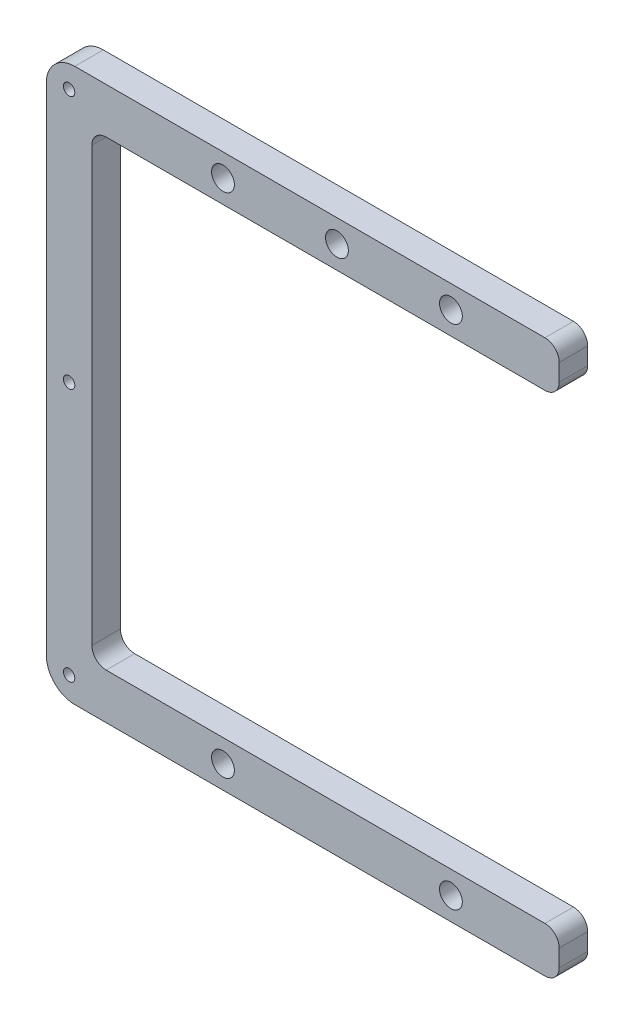
SolidWorks part; units mm, degrees
ref_plane "Front Plane" through (0, 0, 0) normal (0, 0, 1) x (1, 0, 0)
ref_plane "Top Plane" through (0, 0, 0) normal (0, 1, 0) x (1, 0, 0)
ref_plane "Right Plane" through (0, 0, 0) normal (1, 0, 0) x (0, 0, -1)
sketch "Sketch1" plane through (0, 0, 0) normal (0, 0, 1) x (1, 0, 0)
  line L0 (0, -43.5) -> (0, 43.5)
  line L1 (5, 48.5) -> (87.5, 48.5)
  line L2 (90, 46) -> (90, 43)
  line L3 (87.5, 40.5) -> (10.5, 40.5)
  line L4 (8, 38) -> (8, -38)
  line L5 (10.5, -40.5) -> (87.5, -40.5)
  line L7 (87.5, -48.5) -> (5, -48.5)
  line L8 (90, -43) -> (90, -46)
  arc A0 (0, -43.5) -> (5, -48.5) centre (5, -43.5) ccw
  arc A1 (0, 43.5) -> (5, 48.5) centre (5, 43.5) cw
  arc A2 (90, 43) -> (87.5, 40.5) centre (87.5, 43) cw
  arc A3 (87.5, 48.5) -> (90, 46) centre (87.5, 46) cw
  arc A6 (8, -38) -> (10.5, -40.5) centre (10.5, -38) ccw
  arc A7 (10.5, 40.5) -> (8, 38) centre (10.5, 38) ccw
  arc A8 (90, -46) -> (87.5, -48.5) centre (87.5, -46) cw
  arc A9 (90, -43) -> (87.5, -40.5) centre (87.5, -43) ccw
  point P4 (0, 0)
  dimension "D6" = 5
  dimension "D7" = 2.5
  dimension "D9" = 2.5
  dimension "D1" = 89
  dimension "D2" = 8
  dimension "D3" = 8
  dimension "D4" = 8
  dimension "D5" = 90
  dimension "D8" = 0
extrude "Boss-Extrude1" add sketch "Sketch1" along normal blind 5
sketch "Sketch4" plane through (0, 0, 5) normal (0, 0, 1) x (1, 0, 0)
  line L0 (51, 52.0993) -> (51, -52.0993) construction
  line L2 (90, 43) -> (90, 46) construction
  line L3 (90, 44.5) -> (10.5, 44.5) construction
  line L4 (0, 0) -> (111.1347, 0) construction
  line L6 (0, 43.5) -> (0, -43.5) construction
  circle A0 centre (71, 44.5) radius 2
  circle A1 centre (31, 44.5) radius 2
  circle A2 centre (71, -44.5) radius 2
  circle A3 centre (31, -44.5) radius 2
  circle A4 centre (51, 44.5) radius 2
  dimension "D2" = 4
  dimension "D3" = 4
  dimension "D6" = 4
  dimension "D1" = 51
  dimension "D4" = 40
  dimension "D5" = 31
extrude "Cut-Extrude1" cut sketch "Sketch4" against normal through all
sketch "Sketch5" plane through (0, 0, 5) normal (0, 0, 1) x (1, 0, 0)
  line L0 (90, 44.5) -> (-12.5105, 44.5) construction
  line L1 (90, 43) -> (90, 46) construction
  line L2 (90, -44.5) -> (-12.5105, -44.5) construction
  line L3 (90, -46) -> (90, -43) construction
  line L4 (4, 53.2514) -> (4, -51.7153) construction
  circle A0 centre (4, 44.5) radius 1
  circle A1 centre (4, 0) radius 1
  circle A2 centre (4, -44.5) radius 1
  dimension "D2" = 2
  dimension "D3" = 2
  dimension "D4" = 2
  dimension "D1" = 4
extrude "Cut-Extrude2" cut sketch "Sketch5" against normal blind 3
equation "\"38.5mmmm\"=27.8036"
